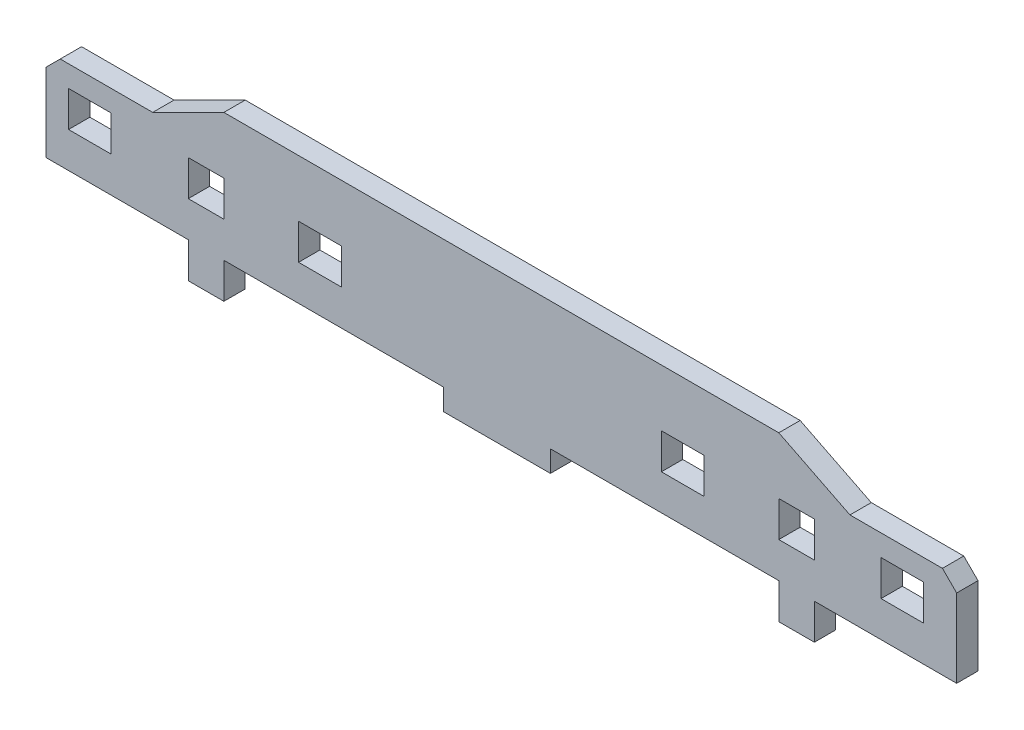
SolidWorks part; units mm, degrees
ref_plane "Front" through (0, 0, 0) normal (0, 0, 1) x (1, 0, 0)
ref_plane "Top" through (0, 0, 0) normal (0, 1, 0) x (1, 0, 0)
ref_plane "Right" through (0, 0, 0) normal (1, 0, 0) x (0, 0, -1)
sketch "Sketch1" plane through (0, 0, 0) normal (0, 0, 1) x (1, 0, 0)
  line L0 (0, 0) -> (-78, 0)
  line L1 (-83, 0) -> (-88, 0)
  line L2 (0, 0) -> (0, -5)
  line L3 (0, -5) -> (5, -5)
  line L4 (5, 0) -> (5, -5)
  line L5 (-88, 0) -> (-88, 13)
  line L6 (-88, 13) -> (-78, 18)
  line L7 (-78, 0) -> (-78, -5)
  line L8 (-78, -5) -> (-83, -5)
  line L9 (-83, 0) -> (-83, -5)
  line L10 (-78, 18) -> (0, 18)
  line L11 (0, 18) -> (10, 13)
  line L12 (10, 13) -> (10, 0)
  line L13 (10, 0) -> (5, 0)
  dimension "D1" = 5
  dimension "D2" = 78
  dimension "D3" = 5
  dimension "D4" = 5
  dimension "D5" = 5
  dimension "D6" = 5
  dimension "D7" = 18
  dimension "D8" = 18
  dimension "D9" = 5
  dimension "D10" = 5
  dimension "D11" = 5
  dimension "D12" = 10
extrude "Boss-Extrude1" add sketch "Sketch1" along normal blind 3
sketch "Sketch3" plane through (0, 0, 3) normal (0, 0, 1) x (1, 0, 0)
  line L0 (-39, 0) -> (-39, 7.477) construction
  line L1 (10, 13) -> (25, 13)
  line L2 (10, 13) -> (10, 0)
  line L3 (10, 0) -> (25, 0)
  line L4 (25, 13) -> (25, 0)
  line L5 (-78, 0) -> (0, 0) construction
  line L6 (-103, 13) -> (-103, 0)
  line L7 (-88, 0) -> (-103, 0)
  line L8 (-88, 13) -> (-88, 0)
  line L9 (-88, 13) -> (-103, 13)
  dimension "D1" = 15
extrude "Boss-Extrude2" add sketch "Sketch3" against normal blind 3
sketch "Sketch2" plane through (0, 0, 3) normal (0, 0, 1) x (1, 0, 0)
  line L0 (-78, 0) -> (0, 0) construction
  line L1 (-67.5, 10) -> (-61.5, 10)
  line L2 (-67.5, 10) -> (-67.5, 5)
  line L3 (-67.5, 5) -> (-61.5, 5)
  line L4 (-61.5, 10) -> (-61.5, 5)
  line L5 (25, 0) -> (25, 13) construction
  line L6 (-39, 0) -> (-39, 7.3389) construction
  line L7 (-16.5, 10) -> (-16.5, 5)
  line L8 (-10.5, 5) -> (-16.5, 5)
  line L9 (-10.5, 10) -> (-10.5, 5)
  line L10 (-10.5, 10) -> (-16.5, 10)
  line L11 (0, 5) -> (0, 10)
  line L12 (-83, 5) -> (-78, 5)
  line L13 (-83, 5) -> (-83, 10)
  line L14 (-83, 10) -> (-78, 10)
  line L15 (-78, 5) -> (-78, 10)
  line L16 (5, 10) -> (0, 10)
  line L17 (5, 5) -> (5, 10)
  line L18 (5, 5) -> (0, 5)
  line L19 (-103, 13) -> (-103, 0) construction
  line L20 (20.37, 10) -> (20.37, 5)
  line L21 (-99.83, 10) -> (-93.83, 10)
  line L22 (-93.83, 10) -> (-93.83, 5)
  line L23 (-99.83, 10) -> (-99.83, 5)
  line L25 (14.37, 5) -> (20.37, 5)
  line L26 (14.37, 10) -> (14.37, 5)
  line L27 (14.37, 10) -> (20.37, 10)
  line L29 (-99.83, 5) -> (-93.83, 5)
  line L30 (-103, 13) -> (-103, 0) construction
  line L31 (-103, 0) -> (-83, 0) construction
  line L32 (5, 0) -> (25, 0) construction
  dimension "D1" = 5
  dimension "D2" = 5
  dimension "D3" = 6
  dimension "D4" = 3.17
  dimension "D5" = 35.5
  dimension "D6" = 5
  dimension "D7" = 5
  dimension "D8" = 20
  dimension "D9" = 5
  dimension "D10" = 5
  dimension "D11" = 5
  dimension "D12" = 6
  dimension "D13" = 4.63
  dimension "D14" = 6
extrude "Cut-Extrude1" cut sketch "Sketch2" against normal blind 3
chamfer "Chamfer1" distance 2 angle 45 2 edges at (-103, 13, 1.5) (25, 13, 1.5)
sketch "Sketch4" plane through (0, 0, 0) normal (0, 0, -1) x (-1, 0, 0)
  line L0 (39.6026, 14.5918) -> (39.6026, -14.5918) construction
  line L1 (78, 0) -> (0, 0) construction
  line L3 (32.1026, 0) -> (47.1026, 0)
  line L4 (47.1026, 0) -> (47.1026, -3)
  line L5 (47.1026, -3) -> (32.1026, -3)
  line L6 (32.1026, -3) -> (32.1026, 0)
  point P5 (39.6026, 0)
  dimension "D1" = 7.5
  dimension "D2" = 3
extrude "Boss-Extrude3" add sketch "Sketch4" against normal blind 3
